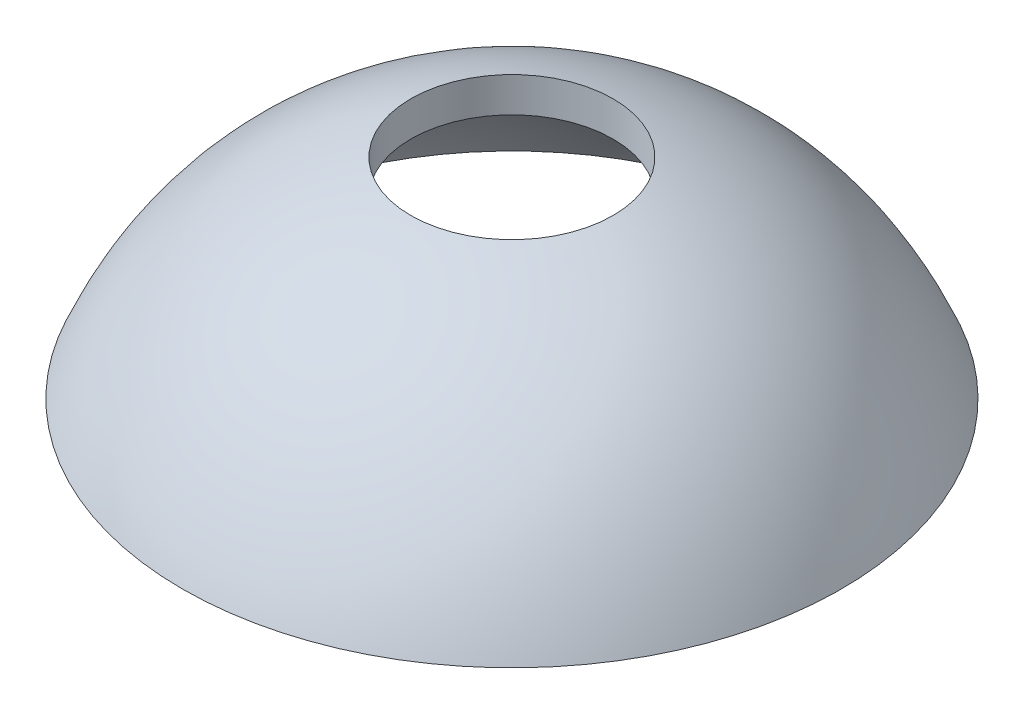
SolidWorks part; units mm, degrees
ref_plane "Front Plane" through (0, 0, 0) normal (0, 0, 1) x (1, 0, 0)
ref_plane "Top Plane" through (0, 0, 0) normal (0, 1, 0) x (1, 0, 0)
ref_plane "Right Plane" through (0, 0, 0) normal (1, 0, 0) x (0, 0, -1)
sketch "Sketch1" plane through (0, 0, 0) normal (0, 0, 1) x (1, 0, 0)
  line L0 (0, 63.1498) -> (0, -78.615) construction
  line L1 (-68.0471, 0) -> (59.799, 0) construction
  line L2 (7.366, 15.24) -> (7.366, 12.7)
  line L3 (22.098, 0) -> (24.003, 0)
  spline S0 degree 2 poles (7.366, 12.7) (17.5707, 9.6997) (22.098, 0) knots 0 0 0 1 1 1
  spline S1 degree 2 poles (7.366, 15.24) (19.1589, 11.7564) (24.003, 0) knots 0 0 0 1 1 1
  point P11 (0, 0)
  point P12 (15.8739, 8.26)
  point P13 (15.8739, 10.9883)
  point P14 (7.366, 13.97)
  dimension "D1" = 7.366
  dimension "D2" = 1.905
  dimension "D3" = 12.7
  dimension "D4" = 2.54
  dimension "D5" = 22.098
revolve "Revolve1" add sketch "Sketch1" angle 360 about L0
